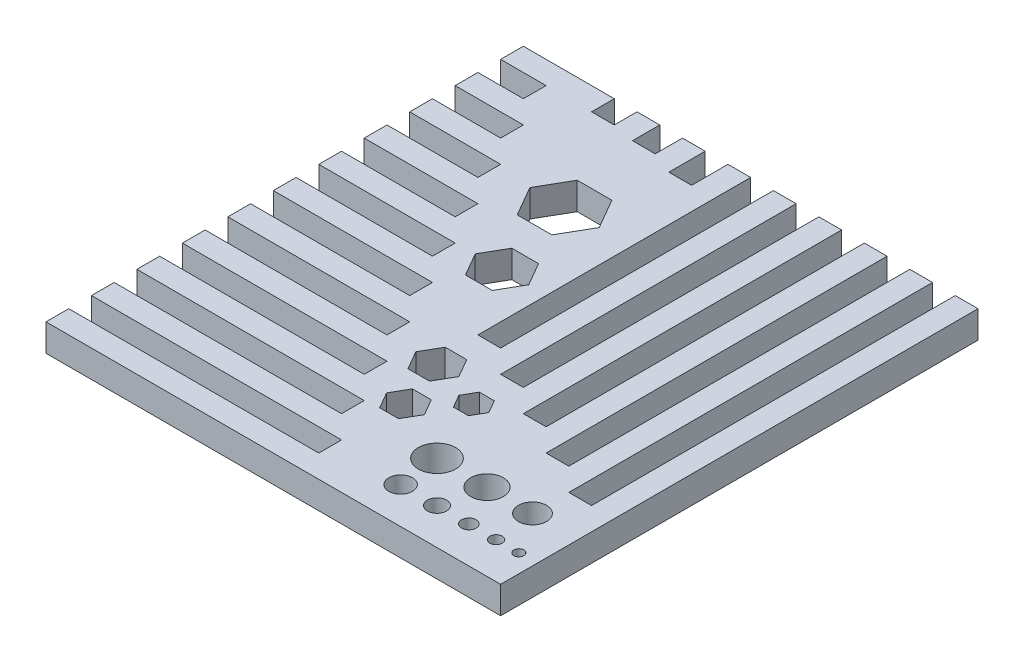
SolidWorks part; units mm, degrees
ref_plane "Front Plane" through (0, 0, 0) normal (0, 0, 1) x (1, 0, 0)
ref_plane "Top Plane" through (0, 0, 0) normal (0, 1, 0) x (1, 0, 0)
ref_plane "Right Plane" through (0, 0, 0) normal (1, 0, 0) x (0, 0, -1)
sketch "Sketch1" plane through (0, 0, 0) normal (0, 1, 0) x (1, 0, 0)
  line L1 (0, 0) -> (100, 0)
  line L2 (0, 0) -> (0, 105)
  line L3 (0, 105) -> (100, 105)
  line L4 (100, 0) -> (100, 105)
  dimension "D1" = 100
  dimension "D2" = 105
extrude "Boss-Extrude1" add sketch "Sketch1" along normal blind 6
sketch "Sketch3" plane through (0, 6, 0) normal (0, 1, 0) x (1, 0, 0)
  line L0 (0, 105) -> (0, 0) construction
  line L1 (0, 100) -> (10, 100)
  line L2 (0, 100) -> (0, 95)
  line L3 (0, 95) -> (10, 95)
  line L4 (10, 100) -> (10, 95)
  line L5 (100, 105) -> (0, 105) construction
  line L6 (0, 90) -> (15, 90)
  line L7 (0, 90) -> (0, 85)
  line L8 (0, 85) -> (15, 85)
  line L9 (15, 90) -> (15, 85)
  line L10 (0, 80) -> (20, 80)
  line L11 (0, 80) -> (0, 75)
  line L12 (0, 75) -> (20, 75)
  line L13 (20, 80) -> (20, 75)
  line L14 (0, 70) -> (25, 70)
  line L15 (0, 70) -> (0, 65)
  line L16 (0, 65) -> (25, 65)
  line L17 (25, 70) -> (25, 65)
  line L18 (0, 60) -> (30, 60)
  line L19 (0, 60) -> (0, 55)
  line L20 (0, 55) -> (30, 55)
  line L21 (30, 60) -> (30, 55)
  line L22 (0, 50) -> (35, 50)
  line L23 (0, 50) -> (0, 45)
  line L24 (0, 45) -> (35, 45)
  line L25 (35, 50) -> (35, 45)
  line L26 (0, 40) -> (40, 40)
  line L27 (0, 40) -> (0, 35)
  line L28 (0, 35) -> (40, 35)
  line L29 (40, 40) -> (40, 35)
  line L30 (0, 30) -> (45, 30)
  line L31 (0, 30) -> (0, 25)
  line L32 (0, 25) -> (45, 25)
  line L33 (45, 30) -> (45, 25)
  line L34 (0, 20) -> (50, 20)
  line L35 (0, 20) -> (0, 15)
  line L36 (0, 15) -> (50, 15)
  line L37 (50, 20) -> (50, 15)
  line L38 (0, 10) -> (55, 10)
  line L39 (0, 10) -> (0, 5)
  line L40 (0, 5) -> (55, 5)
  line L41 (55, 10) -> (55, 5)
  dimension "D1" = 10
  dimension "D2" = 5
  dimension "D3" = 5
  dimension "D4" = 5
  dimension "D5" = 5
  dimension "D6" = 5
  dimension "D7" = 5
  dimension "D8" = 5
  dimension "D9" = 15
  dimension "D10" = 20
  dimension "D11" = 25
  dimension "D12" = 30
  dimension "D13" = 35
  dimension "D14" = 40
  dimension "D15" = 45
  dimension "D16" = 50
  dimension "D17" = 55
extrude "Cut-Extrude1" cut sketch "Sketch3" against normal blind 6
sketch "Sketch4" plane through (0, 6, 0) normal (0, 1, 0) x (1, 0, 0)
  line L0 (100, 105) -> (0, 105) construction
  line L1 (95, 105) -> (90, 105)
  line L2 (95, 105) -> (95, 25)
  line L3 (95, 25) -> (90, 25)
  line L4 (90, 105) -> (90, 25)
  line L5 (100, 0) -> (100, 105) construction
  line L6 (85, 105) -> (80, 105)
  line L7 (85, 105) -> (85, 30)
  line L8 (85, 30) -> (80, 30)
  line L9 (80, 105) -> (80, 30)
  line L10 (75, 105) -> (70, 105)
  line L11 (75, 105) -> (75, 35)
  line L12 (75, 35) -> (70, 35)
  line L13 (70, 105) -> (70, 35)
  line L14 (65, 105) -> (60, 105)
  line L15 (65, 105) -> (65, 40)
  line L16 (65, 40) -> (60, 40)
  line L17 (60, 105) -> (60, 40)
  line L18 (55, 105) -> (50, 105)
  line L19 (55, 105) -> (55, 45)
  line L20 (55, 45) -> (50, 45)
  line L21 (50, 105) -> (50, 45)
  dimension "D1" = 5
  dimension "D2" = 5
  dimension "D3" = 80
  dimension "D4" = 60
  dimension "D5" = 65
  dimension "D6" = 70
  dimension "D7" = 75
extrude "Cut-Extrude2" cut sketch "Sketch4" against normal blind 6
sketch "Sketch5" plane through (0, 6, 0) normal (0, 1, 0) x (1, 0, 0)
  line L0 (100, 0) -> (100, 105) construction
  line L1 (0, 0) -> (100, 0) construction
  circle A0 centre (91, 8) radius 1.35
  circle A1 centre (85, 8) radius 1.6
  circle A2 centre (78, 8) radius 2.1
  circle A3 centre (70, 8) radius 2.6
  circle A4 centre (96, 8) radius 1.1
  circle A5 centre (90, 17) radius 3.1
  circle A6 centre (80, 17) radius 3.6
  circle A7 centre (69, 17) radius 4.1
  dimension "D1" = 2.2
  dimension "D2" = 2.7
  dimension "D3" = 3.2
  dimension "D4" = 4.2
  dimension "D5" = 5.2
  dimension "D6" = 4
  dimension "D7" = 5
  dimension "D8" = 6
  dimension "D9" = 7
  dimension "D10" = 8
  dimension "D12" = 6.2
  dimension "D13" = 7.2
  dimension "D14" = 8.2
  dimension "D15" = 10
  dimension "D11" = 8
  dimension "D16" = 10
  dimension "D17" = 11
  dimension "D18" = 17
extrude "Cut-Extrude3" cut sketch "Sketch5" against normal through all
ref_plane "Plane1" through (0, 6, -105) normal (-1, 0, 0) x (0, 0, 1)
sketch "Sketch7" plane through (0, 6, 0) normal (0, 1, 0) x (1, 0, 0)
  line L0 (50, 105) -> (0, 105) construction
  line L1 (20, 105) -> (25, 105)
  line L2 (20, 105) -> (20, 100)
  line L3 (20, 100) -> (25, 100)
  line L4 (25, 105) -> (25, 100)
  line L5 (50, 105) -> (50, 45) construction
  line L6 (30, 105) -> (35, 105)
  line L7 (30, 105) -> (30, 99)
  line L8 (30, 99) -> (35, 99)
  line L9 (35, 105) -> (35, 99)
  line L10 (40, 105) -> (45, 105)
  line L11 (40, 105) -> (40, 97)
  line L12 (40, 97) -> (45, 97)
  line L13 (45, 105) -> (45, 97)
  dimension "D1" = 5
  dimension "D2" = 5
  dimension "D3" = 5
  dimension "D4" = 5
  dimension "D5" = 5
  dimension "D6" = 5
  dimension "D7" = 5
  dimension "D8" = 6
  dimension "D9" = 8
extrude "Cut-Extrude4" cut sketch "Sketch7" against normal through all
sketch "Sketch8" plane through (0, 6, 0) normal (0, 1, 0) x (1, 0, 0)
  line L1 (65.9861, 31.4169) -> (64.3407, 34.2669)
  line L2 (64.3407, 34.2669) -> (61.0498, 34.2669)
  line L3 (61.0498, 34.2669) -> (59.4043, 31.4169)
  line L4 (59.4043, 31.4169) -> (61.0498, 28.5669)
  line L5 (61.0498, 28.5669) -> (64.3407, 28.5669)
  line L6 (64.3407, 28.5669) -> (65.9861, 31.4169)
  line L7 (59.3096, 23.9217) -> (57.2311, 27.5217)
  line L8 (57.2311, 27.5217) -> (53.0742, 27.5217)
  line L9 (53.0742, 27.5217) -> (50.9957, 23.9217)
  line L10 (50.9957, 23.9217) -> (53.0742, 20.3217)
  line L11 (53.0742, 20.3217) -> (57.2311, 20.3217)
  line L12 (57.2311, 20.3217) -> (59.3096, 23.9217)
  line L13 (55.8455, 34.9721) -> (53.4783, 39.0721)
  line L14 (53.4783, 39.0721) -> (48.7441, 39.0721)
  line L15 (48.7441, 39.0721) -> (46.3769, 34.9721)
  line L16 (46.3769, 34.9721) -> (48.7441, 30.8721)
  line L17 (48.7441, 30.8721) -> (53.4783, 30.8721)
  line L18 (53.4783, 30.8721) -> (55.8455, 34.9721)
  line L19 (46.0376, 60.1512) -> (43.0931, 65.2512)
  line L20 (43.0931, 65.2512) -> (37.2041, 65.2512)
  line L21 (37.2041, 65.2512) -> (34.2596, 60.1512)
  line L22 (34.2596, 60.1512) -> (37.2041, 55.0512)
  line L23 (37.2041, 55.0512) -> (43.0931, 55.0512)
  line L24 (43.0931, 55.0512) -> (46.0376, 60.1512)
  line L25 (42.8841, 78.7936) -> (39.0736, 85.3936)
  line L26 (39.0736, 85.3936) -> (31.4525, 85.3936)
  line L27 (31.4525, 85.3936) -> (27.642, 78.7936)
  line L28 (27.642, 78.7936) -> (31.4525, 72.1936)
  line L29 (31.4525, 72.1936) -> (39.0736, 72.1936)
  line L30 (39.0736, 72.1936) -> (42.8841, 78.7936)
  circle A0 centre (62.6952, 31.4169) radius 2.85 construction
  circle A1 centre (55.1527, 23.9217) radius 3.6 construction
  circle A2 centre (51.1112, 34.9721) radius 4.1 construction
  circle A3 centre (40.1486, 60.1512) radius 5.1 construction
  circle A4 centre (35.2631, 78.7936) radius 6.6 construction
  dimension "D1" = 5.7
  dimension "D2" = 7.2
  dimension "D3" = 8.2
  dimension "D4" = 10.2
  dimension "D5" = 13.2
extrude "Cut-Extrude5" cut sketch "Sketch8" against normal through all
